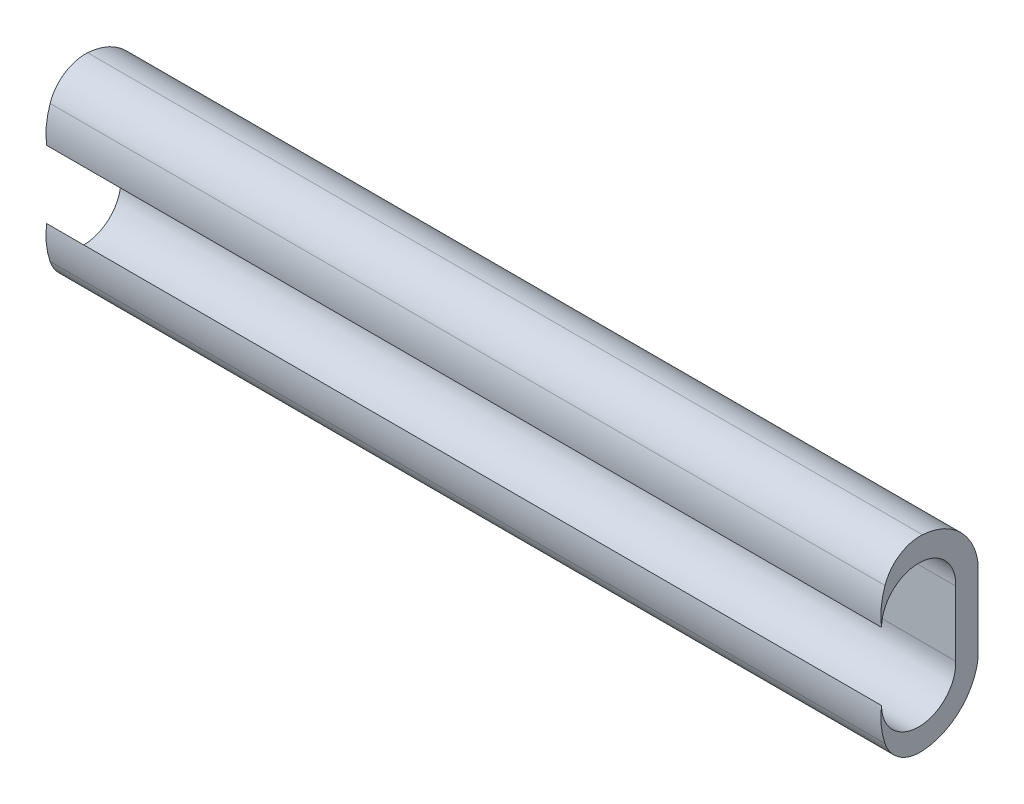
SolidWorks part; units mm, degrees
ref_plane "Front Plane" through (0, 0, 0) normal (0, 0, 1) x (1, 0, 0)
ref_plane "Top Plane" through (0, 0, 0) normal (0, 1, 0) x (1, 0, 0)
ref_plane "Right Plane" through (0, 0, 0) normal (1, 0, 0) x (0, 0, -1)
sketch "Sketch1" plane through (0, 0, 0) normal (1, 0, 0) x (0, 0, -1)
  line L1 (0, 0) -> (1.2, 0)
  line L2 (0, 0) -> (0, 1.8951)
  line L4 (1.2, 0) -> (1.2, 2.25)
  circle A0 centre (-1.9987, 1.8239) radius 2
  arc A1 (1.2, 2.25) -> (-1.7914, 5.0442) centre (-1.9987, 1.8239) ccw
  arc A2 (-3.815, 3.6876) -> (-1.7914, 5.0442) centre (-1.9199, 3.0484) cw
  spline S0 degree 3 poles (-3.815, 3.6876) (-4.1426, 2.7163) (-4.1034, 1.7138) (-3.7131, 0.794) knots 0.271846 0.271846 0.271846 0.271846 1 1 1 1
  dimension "D1" = 2
extrude "Boss-Extrude1" add sketch "Sketch1" against normal blind 45 contours A2 S0 A0 L2 L1 L4 A1
mirror "Mirror1" about plane through (-45, 0, 0) normal (0, -1, 0) of bodies 101
